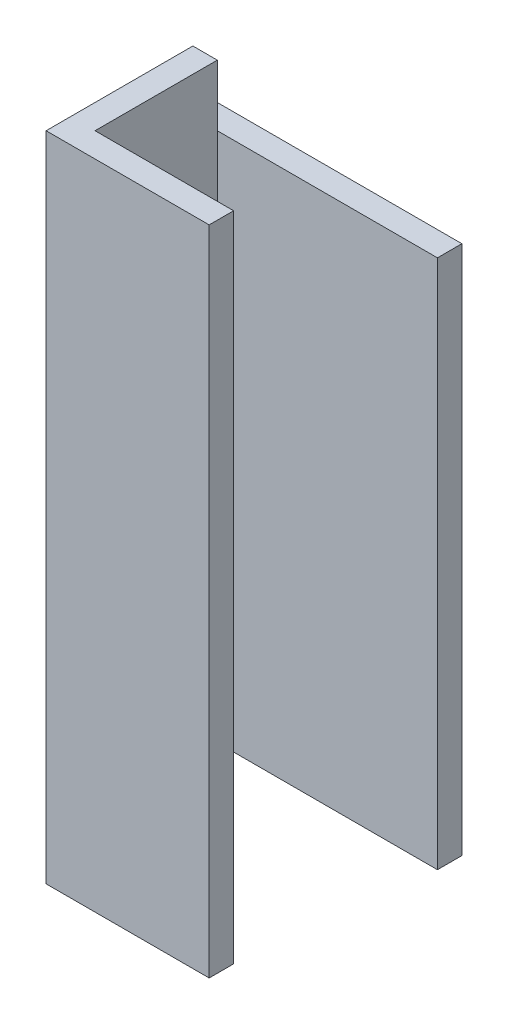
SolidWorks part; units mm, degrees
ref_plane "Front Plane" through (0, 0, 0) normal (0, 0, 1) x (1, 0, 0)
ref_plane "Top Plane" through (0, 0, 0) normal (0, 1, 0) x (1, 0, 0)
ref_plane "Right Plane" through (0, 0, 0) normal (1, 0, 0) x (0, 0, -1)
sketch "Sketch1" plane through (0, 0, 0) normal (0, 1, 0) x (1, 0, 0)
  line L1 (0, -0.105) -> (0.3, -0.105)
  line L2 (0, -0.105) -> (0, 0.105)
  line L3 (0, 0.105) -> (0.3, 0.105)
  line L4 (0.3, -0.105) -> (0.3, 0.105)
  line L5 (0, -0.105) -> (0.3, 0.105) construction
  line L6 (0, 0.105) -> (0.3, -0.105) construction
  point P0 (0.15, 0)
  point P5 (0, 0)
  dimension "D1" = 0.3
  dimension "D2" = 0.21
extrude "Boss-Extrude1" add sketch "Sketch1" along normal mid plane 0.8
sketch "Sketch2" plane through (0, -0.4, 0) normal (0, -1, 0) x (1, 0, 0)
  line L0 (0.3, 0.105) -> (0.3, -0.105) construction
  line L1 (0.3, 0.075) -> (0.03, 0.075)
  line L2 (0.3, 0.075) -> (0.3, -0.075)
  line L3 (0.3, -0.075) -> (0.03, -0.075)
  line L4 (0.03, 0.075) -> (0.03, -0.075)
  line L5 (0, 0.105) -> (0.3, 0.105) construction
  line L6 (0.3, -0.105) -> (0, -0.105) construction
  line L7 (0, -0.105) -> (0, 0.105) construction
  dimension "D1" = 0.03
  dimension "D2" = 0.03
  dimension "D3" = 0.03
extrude "Cut-Extrude1" cut sketch "Sketch2" against normal through all
sketch "Sketch3" plane through (0, -0.4, 0) normal (0, -1, 0) x (1, 0, 0)
  line L0 (0.3, 0.075) -> (0.03, 0.075) construction
  line L1 (0.3, 0.105) -> (0.2, 0.105)
  line L2 (0.3, 0.105) -> (0.3, 0.075)
  line L3 (0.3, 0.075) -> (0.2, 0.075)
  line L4 (0.2, 0.105) -> (0.2, 0.075)
  line L5 (0, -0.105) -> (0, 0.105) construction
  dimension "D1" = 0.2
extrude "Cut-Extrude2" cut sketch "Sketch3" against normal through all
sketch "Sketch4" plane through (0, 0, -0.105) normal (0, 0, -1) x (-1, 0, 0)
  line L0 (-0.3, 0.4) -> (-0.3, -0.4) construction
  line L1 (0, -0.4) -> (-0.3, -0.4)
  line L2 (0, -0.4) -> (0, -0.325)
  line L3 (0, -0.325) -> (-0.3, -0.325)
  line L4 (-0.3, -0.4) -> (-0.3, -0.325)
  dimension "D1" = 0.075
extrude "Cut-Extrude3" cut sketch "Sketch4" against normal blind 0.03
mirror "Mirror1" about plane through (0, 0, 0) normal (0, 1, 0) of "Cut-Extrude3"
